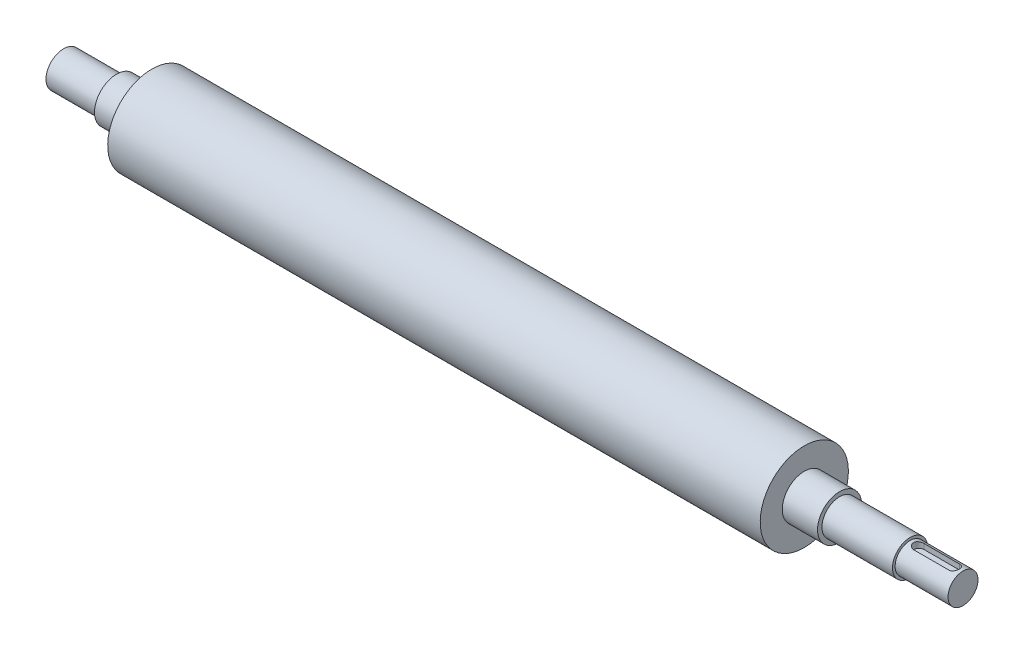
SolidWorks part; units mm, degrees
ref_plane "前视基准面" through (0, 0, 0) normal (0, 0, 1) x (1, 0, 0)
ref_plane "上视基准面" through (0, 0, 0) normal (0, 1, 0) x (1, 0, 0)
ref_plane "右视基准面" through (0, 0, 0) normal (1, 0, 0) x (0, 0, -1)
sketch "草图1" plane through (0, 0, 0) normal (0, 0, 1) x (1, 0, 0)
  line L0 (-230.7094, 0) -> (459.7941, 0) construction
  line L1 (0, 215.5466) -> (0, -189.8195) construction
  line L2 (-185, 25) -> (185, 25)
  line L6 (-235, 10) -> (-235, 0)
  line L7 (-205, 10) -> (-235, 10)
  line L8 (-185, 25) -> (-185, 12.5)
  line L9 (-235, 0) -> (235, 0)
  line L10 (-205, 10) -> (-205, 12.5)
  line L11 (-205, 12.5) -> (-185, 12.5)
  line L13 (205, 10) -> (245, 10)
  line L14 (205, 10) -> (205, 12.5)
  line L15 (205, 12.5) -> (185, 12.5)
  line L16 (185, 25) -> (185, 12.5)
  line L18 (275, 8.5) -> (275, 0)
  line L19 (235, 0) -> (275, 0)
  line L20 (245, 10) -> (245, 8.5)
  line L21 (245, 8.5) -> (275, 8.5)
  point P17 (0, 25)
  dimension "D1" = 12.5
  dimension "D2" = 10
  dimension "D3" = 25
  dimension "D4" = 370
  dimension "D5" = 30
  dimension "D6" = 470
  dimension "D7" = 8.5
  dimension "D8" = 30
  dimension "D9" = 410
  dimension "D10" = 40
revolve "旋转1" add sketch "草图1" angle 360 about L9
ref_plane "基准面1" through (0, 8.5, 0) normal (0, 1, 0) x (1, 0, 0)
sketch "草图2" plane through (0, 8.5, 0) normal (0, 1, 0) x (1, 0, 0)
  line L0 (250, 0) -> (270, 0) construction
  line L1 (250, 3) -> (270, 3)
  line L2 (250, -3) -> (270, -3)
  line L3 (275, -8.5) -> (275, 8.5) construction
  line L4 (245, -8.5) -> (245, 8.5) construction
  arc A0 (250, 3) -> (250, -3) centre (250, 0) ccw
  arc A1 (270, -3) -> (270, 3) centre (270, 0) ccw
  point P2 (260, 0)
  dimension "D1" = 5
  dimension "D2" = 5
  dimension "D3" = 6
  dimension "D4" = 0
extrude "切除-拉伸1" cut sketch "草图2" against normal blind 3.5
